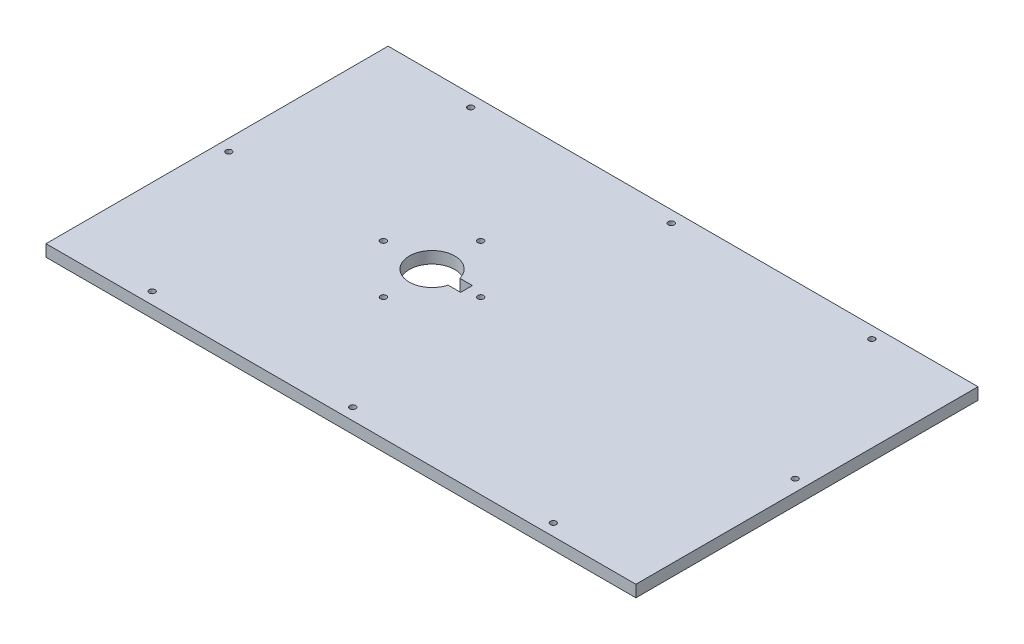
SolidWorks part; units mm, degrees
material "Acrylic (Medium-high impact)"
ref_plane "Front Plane" through (0, 0, 0) normal (0, 0, 1) x (1, 0, 0)
ref_plane "Top Plane" through (0, 0, 0) normal (0, 1, 0) x (1, 0, 0)
ref_plane "Right Plane" through (0, 0, 0) normal (1, 0, 0) x (0, 0, -1)
sketch "Sketch1" plane through (0, 0, 0) normal (0, 1, 0) x (1, 0, 0)
  line L1 (-250, -145) -> (250, -145)
  line L2 (-250, -145) -> (-250, 145)
  line L3 (-250, 145) -> (250, 145)
  line L4 (250, -145) -> (250, 145)
  line L5 (-250, -145) -> (250, 145) construction
  line L6 (-250, 145) -> (250, -145) construction
  line L7 (-240, -135) -> (240, -135) construction
  line L8 (-240, -135) -> (-240, 135) construction
  line L9 (-240, 135) -> (240, 135) construction
  line L10 (240, -135) -> (240, 135) construction
  line L11 (-240, -135) -> (240, 135) construction
  line L12 (-240, 135) -> (240, -135) construction
  line L13 (-317.3233, 0) -> (323.4582, 0) construction
  line L14 (-49.191, -5) -> (-38.5303, -5)
  line L16 (-49.191, 5) -> (-38.5303, 5)
  line L17 (-38.5303, -5) -> (-38.5303, 5)
  circle A0 centre (-240, 0) radius 2.5
  circle A1 centre (-67.7803, 0) radius 41.25 construction
  circle A2 centre (-170, -135) radius 2.5
  circle A3 centre (-170, 135) radius 2.5
  circle A4 centre (170, 135) radius 2.5
  circle A5 centre (240, 0) radius 2.5
  circle A6 centre (170, -135) radius 2.5
  circle A7 centre (0, 135) radius 2.5
  circle A8 centre (0, -135) radius 2.5
  circle A9 centre (-26.5303, 0) radius 2.5
  circle A10 centre (-67.7803, -41.25) radius 2.5
  circle A11 centre (-109.0303, 0) radius 2.5
  circle A12 centre (-67.7803, 41.25) radius 2.5
  arc A13 (-49.191, 5) -> (-49.191, -5) centre (-67.7803, 0) ccw
  point P13 (-48.5303, 0)
  point P38 (-67.7803, 0)
  dimension "D7" = 5
  dimension "D8" = 5
  dimension "D9" = 5
  dimension "D10" = 5
  dimension "D11" = 145
  dimension "D12" = 5
  dimension "D13" = 5
  dimension "D14" = 5
  dimension "D15" = 5
  dimension "D22" = 480
  dimension "D23" = 270
  dimension "D25" = 5
  dimension "D26" = 4
  dimension "D27" = 38.5
  dimension "D29" = 10
  dimension "D30" = 182.2197
  dimension "D28" = 10
  dimension "D24" = 82.5
  dimension "D1" = 290
  dimension "D2" = 500
  dimension "D3" = 10
  dimension "D4" = 10
  dimension "D5" = 250
  dimension "D6" = 145
  dimension "D16" = 80
  dimension "D17" = 80
  dimension "D18" = 80
  dimension "D19" = 80
  dimension "D20" = 250
  dimension "D21" = 250
extrude "Boss-Extrude1" add sketch "Sketch1" along normal blind 10
